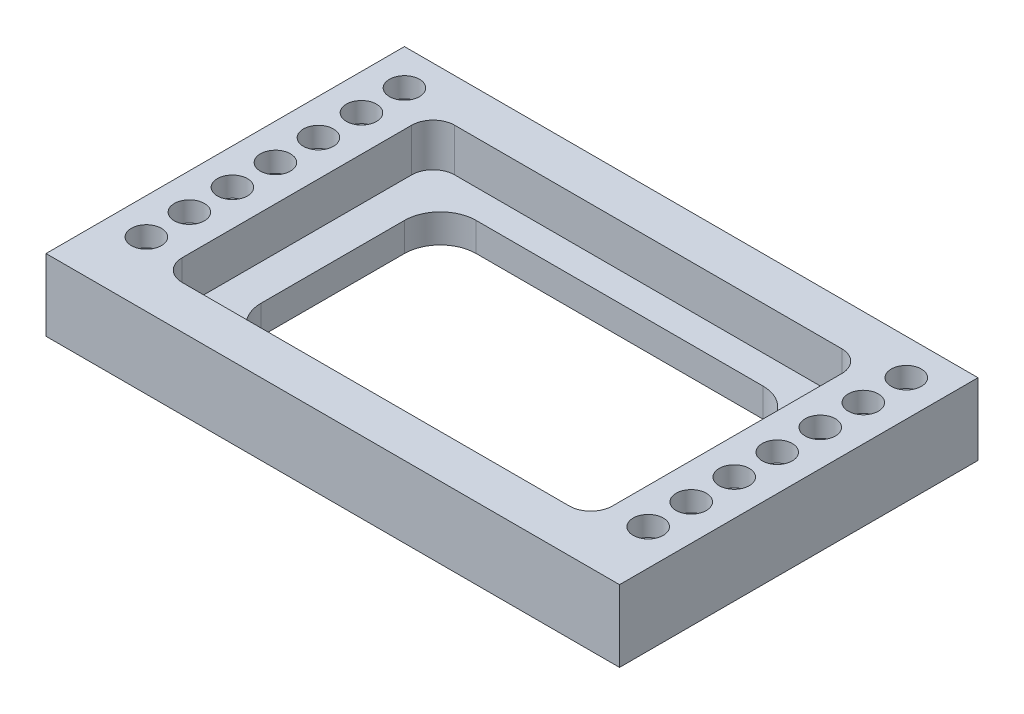
SolidWorks part; units mm, degrees
ref_plane "Alzado" through (0, 0, 0) normal (0, 0, 1) x (1, 0, 0)
ref_plane "Planta" through (0, 0, 0) normal (0, 1, 0) x (1, 0, 0)
ref_plane "Vista lateral" through (0, 0, 0) normal (1, 0, 0) x (0, 0, -1)
sketch "Croquis1" plane through (0, 0, 0) normal (0, 1, 0) x (1, 0, 0)
  line L1 (-200, 125) -> (200, 125)
  line L2 (-200, 125) -> (-200, -125)
  line L3 (-200, -125) -> (200, -125)
  line L4 (200, 125) -> (200, -125)
  line L5 (-200, 125) -> (200, -125) construction
  line L6 (-200, -125) -> (200, 125) construction
  line L7 (-100, 75) -> (100, 75)
  line L8 (-125, 50) -> (-125, -50)
  line L9 (-100, -75) -> (100, -75)
  line L10 (125, 50) -> (125, -50)
  line L11 (-125, 75) -> (125, -75) construction
  line L12 (-125, -75) -> (125, 75) construction
  arc A0 (100, -75) -> (125, -50) centre (100, -50) ccw
  arc A1 (100, 75) -> (125, 50) centre (100, 50) cw
  arc A2 (-125, -50) -> (-100, -75) centre (-100, -50) ccw
  arc A3 (-100, 75) -> (-125, 50) centre (-100, 50) ccw
  point P0 (0, 0)
  point P6 (0, 0)
  dimension "D5" = 25
  dimension "D1" = 400
  dimension "D2" = 250
  dimension "D3" = 250
  dimension "D4" = 150
extrude "Saliente-Extruir1" add sketch "Croquis1" along normal blind 50
sketch "Croquis2" plane through (0, 50, 0) normal (0, 1, 0) x (1, 0, 0)
  line L1 (-135, 95) -> (135, 95)
  line L2 (-150, 80) -> (-150, -80)
  line L3 (-135, -95) -> (135, -95)
  line L4 (150, 80) -> (150, -80)
  line L5 (-150, 95) -> (150, -95) construction
  line L6 (-150, -95) -> (150, 95) construction
  arc A0 (135, 95) -> (150, 80) centre (135, 80) cw
  arc A1 (135, -95) -> (150, -80) centre (135, -80) ccw
  arc A2 (-150, -80) -> (-135, -95) centre (-135, -80) ccw
  arc A3 (-135, 95) -> (-150, 80) centre (-135, 80) ccw
  point P0 (0, 0)
  dimension "D3" = 15
  dimension "D1" = 300
  dimension "D2" = 190
extrude "Cortar-Extruir1" cut sketch "Croquis2" against normal blind 30
hole_wizard "Taladro1" positions "Croquis3" profile "Croquis4" legacy
sketch "Croquis3" plane through (0, 50, 0) normal (0, 1, 0) x (1, 0, 0)
  point P0 (-175, 100)
  dimension "D1" = 175
  dimension "D2" = 100
sketch "Croquis4" plane through (-175, 50, -100) normal (1, 0, 0) x (0, 0, 1)
  line L0 (0, 0) -> (0, 49.8773)
  line L1 (0, 49.8773) -> (7, 49.8773)
  line L2 (7, 49.8773) -> (7, 14)
  line L3 (7, 14) -> (10.5, 14)
  line L4 (10.5, 14) -> (10.5, 0)
  line L5 (10.5, 0) -> (0, 0)
  line L6 (0, 110) -> (0, -10) construction
  dimension "Diámetro" = 14
  dimension "Profundidad" = 50
  dimension "Diámetro de refrentado 1" = 21
  dimension "Profundidad de refrentado 1" = 14
pattern_linear "MatrizL1" count 7 spacing 30 along (0, 0, 1) of "Taladro1"
mirror "Simetría1" about plane through (0, 0, 0) normal (1, 0, 0) of "MatrizL1", "Taladro1"
